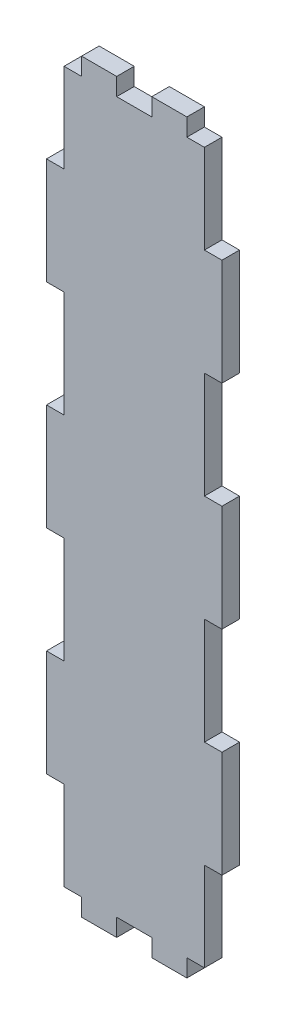
SolidWorks part; units mm, degrees
ref_plane "Front Plane" through (0, 0, 0) normal (0, 0, 1) x (1, 0, 0)
ref_plane "Top Plane" through (0, 0, 0) normal (0, 1, 0) x (1, 0, 0)
ref_plane "Right Plane" through (0, 0, 0) normal (1, 0, 0) x (0, 0, -1)
sketch "Buitenafmeting Rechthoek" plane through (0, 0, 0) normal (0, 0, 1) x (1, 0, 0)
  line L1 (0, 0) -> (40, 0)
  line L2 (0, 0) -> (0, 170)
  line L3 (0, 170) -> (40, 170)
  line L4 (40, 0) -> (40, 170)
  dimension "D1" = 40
  dimension "D2" = 170
extrude "Plaat" add sketch "Buitenafmeting Rechthoek" against normal blind 4
sketch "Tand Hor" plane through (0, 0, 0) normal (0, 0, 1) x (1, 0, 0)
  line L1 (40, 170) -> (0, 170) construction
  line L2 (0, 170) -> (8, 170)
  line L3 (0, 170) -> (0, 166)
  line L4 (0, 166) -> (8, 166)
  line L6 (8, 170) -> (8, 166)
  dimension "D2" = 8
  dimension "D3" = 0
extrude "Tand Boven" cut sketch "Tand Hor" against normal through all
pattern_linear "Tanden Patroon Boven" count 3 spacing 16 along (1, 0, 0) of "Tand Boven"
sketch "Tand Ver" plane through (0, 0, 0) normal (0, 0, 1) x (1, 0, 0)
  line L0 (0, 166) -> (0, 0) construction
  line L1 (0, 170) -> (4, 170)
  line L2 (0, 170) -> (0, 145.7143)
  line L3 (0, 145.7143) -> (4, 145.7143)
  line L4 (4, 170) -> (4, 145.7143)
  dimension "D2" = 24.2857
  dimension "D3" = 170
extrude "Tand Links" cut sketch "Tand Ver" against normal through all
pattern_linear "Tanden Patroon Links" count 4 spacing 48.5714 along (0, -1, 0) of "Tand Links"
sketch "Tand O" plane through (0, 0, 0) normal (0, 0, 1) x (1, 0, 0)
  line L0 (4, 0) -> (40, 0) construction
  line L1 (0, 0) -> (8, 0)
  line L2 (0, 0) -> (0, 4)
  line L3 (0, 4) -> (8, 4)
  line L4 (8, 0) -> (8, 4)
  dimension "D2" = 8
  dimension "D3" = 0
extrude "Tand Onder" cut sketch "Tand O" against normal through all
pattern_linear "Tanden Patroon Onder" count 3 spacing 16 along (1, 0, 0) of "Tand Onder"
sketch "Tand R" plane through (0, 0, 0) normal (0, 0, 1) x (1, 0, 0)
  line L0 (40, 4) -> (40, 166) construction
  line L1 (40, 170) -> (36, 170)
  line L2 (40, 170) -> (40, 145.7143)
  line L3 (40, 145.7143) -> (36, 145.7143)
  line L4 (36, 170) -> (36, 145.7143)
  dimension "D2" = 24.2857
  dimension "D3" = 170
extrude "Tand Rechts" cut sketch "Tand R" against normal through all
pattern_linear "Tanden Patroon Rechts" count 4 spacing 48.5714 along (0, -1, 0) of "Tand Rechts"
equation "\"D1@Buitenafmeting Rechthoek\"= \"Lengte\""
equation "\"D2@Buitenafmeting Rechthoek\" = \"Hoogte\""
equation "\"D1@Plaat\" = \"Dikte\""
equation "\"D3@Tanden Patroon Boven\" = \"LengteHorTand\" * 2"
equation "\"D1@Tanden Patroon Boven\" = \"nPatroonHor\""
equation "\"LengteHorTand\"= \"Lengte\" / \"nHor\"'Spatie tussen verschillende tanden in de lengte"
equation "\"nPatroonHor\"= ( \"nHor\" + 1 ) / 2 - \"GrensHor\"'Aantal kopies van tanden in de lengte"
equation "\"D1@Tand Hor\" = \"Dikte\""
equation "\"D2@Tand Hor\" = \"LengteHorTand\""
equation "\"D1@Tand Ver\" = \"Dikte\""
equation "\"LengteVertTand\"= \"Hoogte\" / \"nVert\"'Spatie tussen verschillende tanden in de hoogte"
equation "\"nPatroonVert\"= ( \"nVert\" + 1 ) / 2 - \"GrensVert\"'Aantal kopies van tanden in de hoogte"
equation "\"D2@Tand Ver\"=\"LengteVertTand\""
equation "\"D3@Tanden Patroon Links\"=\"LengteVertTand\"*2"
equation "\"D3@Tanden Patroon Rechts\"=\"LengteVertTand\"*2"
equation "\"D1@Tanden Patroon Rechts\"=\"nPatroonVert\""
equation "\"D3@Tanden Patroon Onder\"=\"LengteHorTand\"*2"
equation "\"D1@Tanden Patroon Onder\"=\"nPatroonHor\""
equation "\"D1@Tanden Patroon Links\"=\"nPatroonVert\""
equation "\"D3@Tand Ver\"=\"Hoogte\"-\"GrensVert\"*\"LengteVertTand\""
equation "\"D2@Tand R\" = \"LengteVertTand\""
equation "\"D3@Tand R\" = \"Hoogte\" - \"GrensVert\" * \"LengteVertTand\""
equation "\"D2@Tand O\"=\"LengteHorTand\""
equation "\"D3@Tand Hor\"=\"GrensHor\"*\"LengteHorTand\""
equation "\"D3@Tand O\"=\"GrensHor\"*\"LengteHorTand\""
equation "\"Tand Boven\"= IIF ( \"plaatsTandenBoven\" , \"unsuppressed\" , \"suppressed\" )"
equation "\"Tanden Patroon Boven\"= IIF ( \"plaatsTandenBoven\" , \"unsuppressed\" , \"suppressed\" )"
equation "\"Tand Links\"= IIF ( \"plaatsTandenLinks\" , \"unsuppressed\" , \"suppressed\" )"
equation "\"Tanden Patroon Links\"= IIF ( \"plaatsTandenLinks\" , \"unsuppressed\" , \"suppressed\" )"
equation "\"Tand Onder\"= IIF ( \"plaatsTandenOnder\" , \"unsuppressed\" , \"suppressed\" )"
equation "\"Tanden Patroon Onder\"= IIF ( \"plaatsTandenOnder\" , \"unsuppressed\" , \"suppressed\" )"
equation "\"Tand Rechts\"= IIF ( \"plaatsTandenRechts\" , \"unsuppressed\" , \"suppressed\" )"
equation "\"Tanden Patroon Rechts\"= IIF ( \"plaatsTandenRechts\" , \"unsuppressed\" , \"suppressed\" )"
equation "\"D1@Tand O\"=\"Dikte\""
equation "\"D1@Tand R\"=\"Dikte\""
